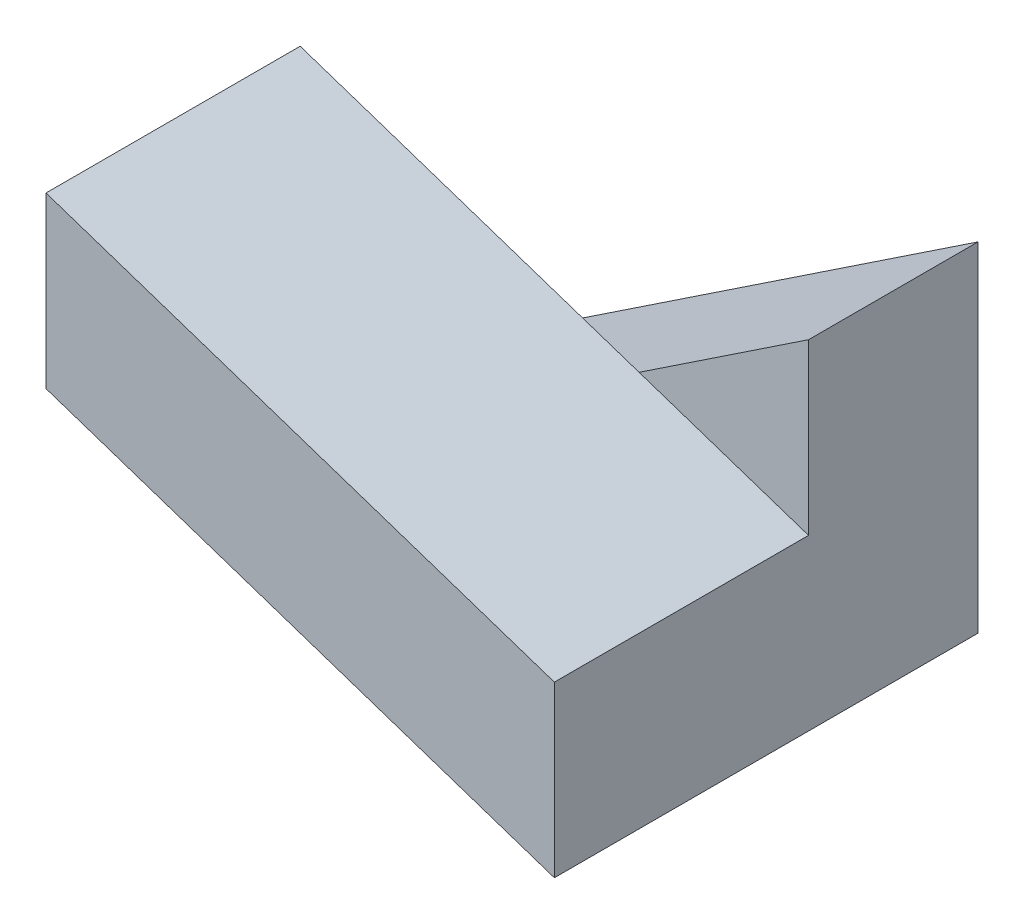
SolidWorks part; units mm, degrees
ref_plane "Front Plane" through (0, 0, 0) normal (0, 0, 1) x (1, 0, 0)
ref_plane "Top Plane" through (0, 0, 0) normal (0, 1, 0) x (1, 0, 0)
ref_plane "Right Plane" through (0, 0, 0) normal (1, 0, 0) x (0, 0, -1)
sketch "Sketch1" plane through (0, 0, 0) normal (0, 0, 1) x (1, 0, 0)
  line L0 (-30, 0) -> (0, 0)
  line L1 (0, 0) -> (0, 20)
  line L2 (0, 20) -> (-30, 0)
  dimension "D1" = 30
  dimension "D2" = 20
extrude "Boss-Extrude1" add sketch "Sketch1" along normal blind 10
sketch "Sketch2" plane through (0, 0, 10) normal (0, 0, 1) x (1, 0, 0)
  line L0 (0, 10) -> (0, 0)
  line L1 (0, 0) -> (0, 20) construction
  line L2 (0, 0) -> (-30, 10)
  line L3 (-30, 10) -> (-30, 20)
  line L4 (-30, 20) -> (0, 10)
  dimension "D1" = 10
  dimension "D2" = 30
  dimension "D3" = 10
extrude "Boss-Extrude2" add sketch "Sketch2" along normal blind 15
